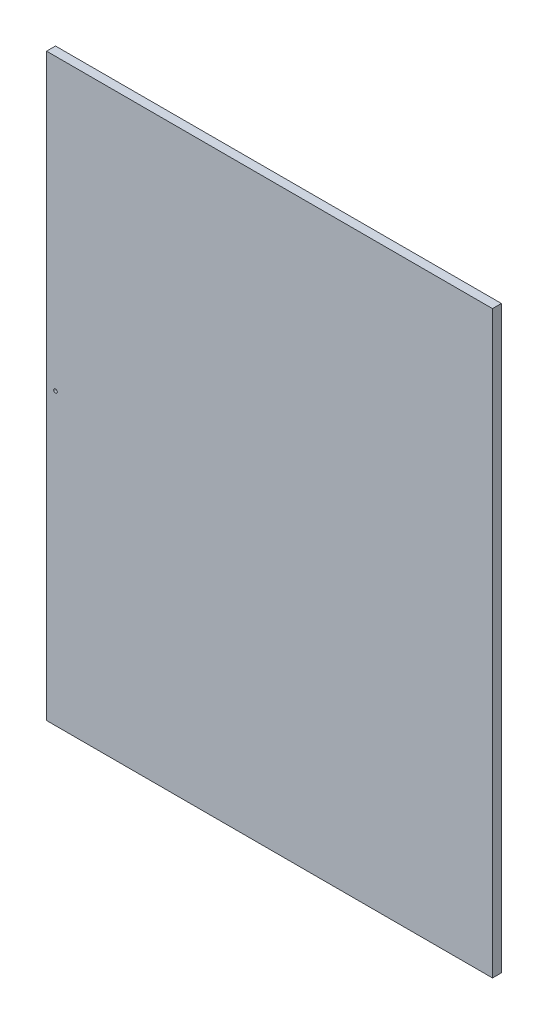
SolidWorks part; units mm, degrees
ref_plane "前视基准面" through (0, 0, 0) normal (0, 0, 1) x (1, 0, 0)
ref_plane "上视基准面" through (0, 0, 0) normal (0, 1, 0) x (1, 0, 0)
ref_plane "右视基准面" through (0, 0, 0) normal (1, 0, 0) x (0, 0, -1)
sketch "草图1" plane through (0, 0, 0) normal (0, 0, 1) x (1, 0, 0)
  line L0 (0, 0) -> (0, 650)
  line L1 (0, 650) -> (500, 650)
  line L2 (500, 650) -> (500, 0)
  line L3 (500, 0) -> (0, 0)
  line L4 (0, 325) -> (10, 325) construction
  circle A0 centre (10, 325) radius 2
  dimension "D5" = 4
  dimension "D1" = 650
  dimension "D2" = 500
  dimension "D3" = 650
  dimension "D4" = 10
extrude "凸台-拉伸1" add sketch "草图1" along normal blind 10
